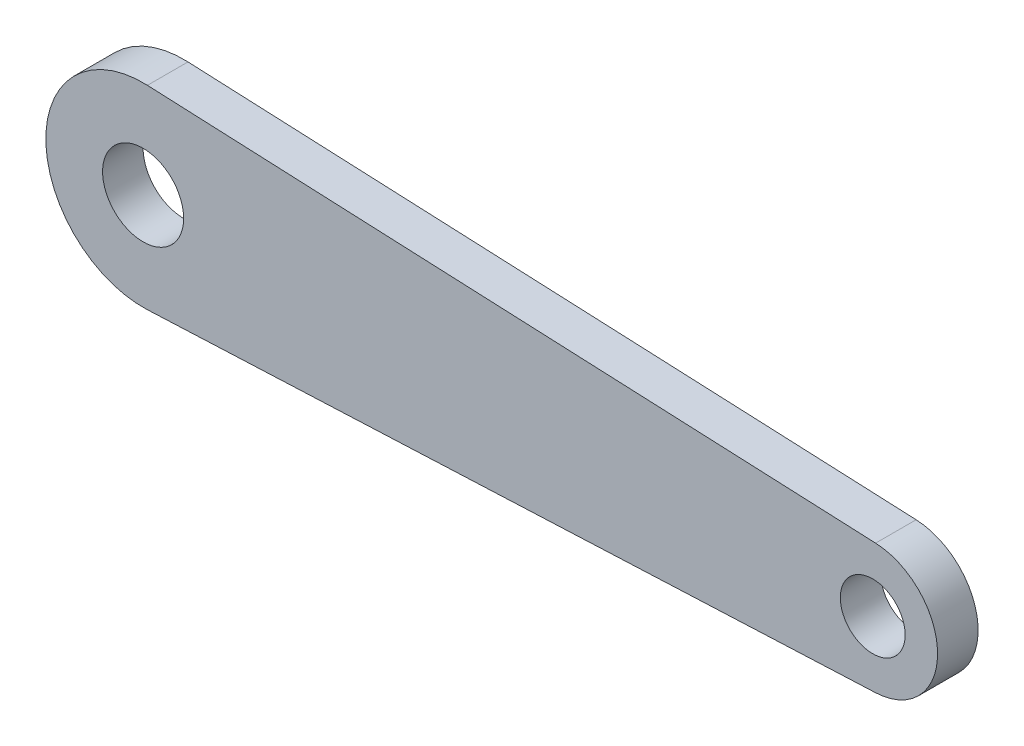
SolidWorks part; units mm, degrees
material "PE High Density"
ref_plane "Front Plane" through (0, 0, 0) normal (0, 0, 1) x (1, 0, 0)
ref_plane "Top Plane" through (0, 0, 0) normal (0, 1, 0) x (1, 0, 0)
ref_plane "Right Plane" through (0, 0, 0) normal (1, 0, 0) x (0, 0, -1)
sketch "Sketch1" plane through (0, 0, 0) normal (0, 0, 1) x (1, 0, 0)
  line L0 (0, -994.956) -> (0, 48752.8433) construction
  line L1 (0.3387, 7.6125) -> (57.3758, 5.075)
  line L2 (57.3758, -5.075) -> (0.3387, -7.6125)
  arc A0 (0.3387, 7.6125) -> (0.3387, -7.6125) centre (0, 0) ccw
  arc A2 (57.3758, -5.075) -> (57.3758, 5.075) centre (57.15, 0) ccw
  circle A4 centre (0, 0) radius 3.175
  circle A5 centre (57.15, 0) radius 2.54
  dimension "D1" = 10.16
  dimension "D3" = 7.62
  dimension "D4" = 6.35
  dimension "D5" = 5.08
  dimension "D2" = 57.15
extrude "Boss-Extrude1" add sketch "Sketch1" along normal blind 3.175
